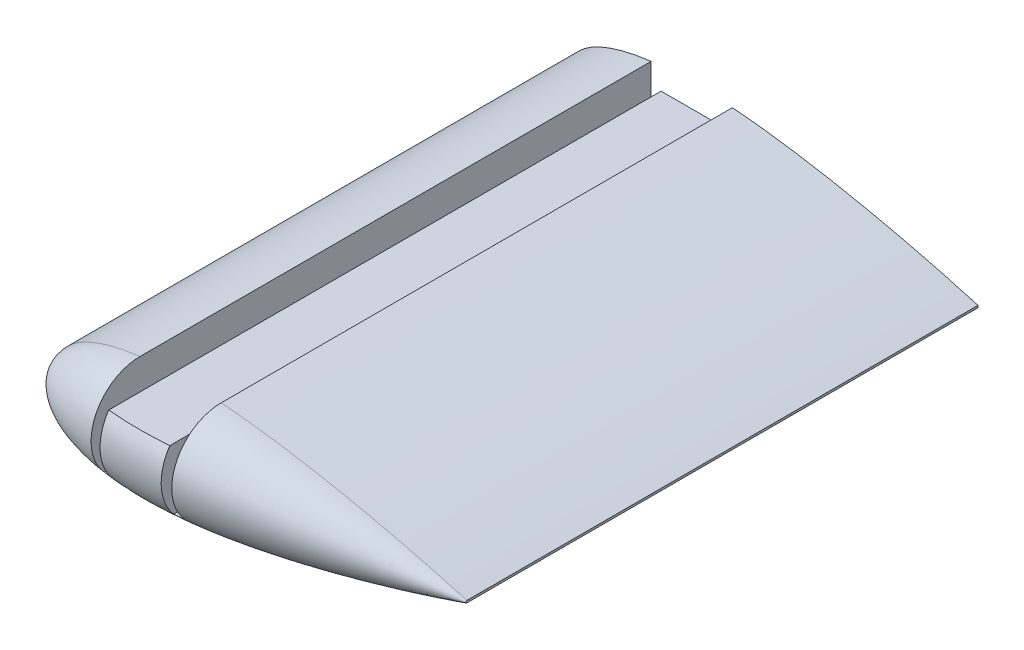
SolidWorks part; units mm, degrees
ref_plane "Спереди" through (0, 0, 0) normal (0, 0, 1) x (1, 0, 0)
ref_plane "Сверху" through (0, 0, 0) normal (0, 1, 0) x (1, 0, 0)
ref_plane "Справа" through (0, 0, 0) normal (1, 0, 0) x (0, 0, -1)
other "Configuration Table"
curve "Curve1"
  spline degree 3 poles (1, 0.0026, 0) (0.9995, 0.0028, 0) (0.9974, 0.0034, 0) (0.9928, 0.0047, 0) (0.9852, 0.0069, 0) (0.9746, 0.01, 0) (0.961, 0.0138, 0) (0.9446, 0.0183, 0) (0.9255, 0.0235, 0) (0.9037, 0.0292, 0) (0.8794, 0.0355, 0) (0.8529, 0.0421, 0) (0.8241, 0.0491, 0) (0.7933, 0.0562, 0) (0.7607, 0.0635, 0) (0.7266, 0.0709, 0) (0.691, 0.0782, 0) (0.6542, 0.0854, 0) (0.6165, 0.0923, 0) (0.5781, 0.0988, 0) (0.5392, 0.1049, 0) (0.5, 0.1104, 0) (0.4609, 0.1152, 0) (0.422, 0.1192, 0) (0.3836, 0.1222, 0) (0.3458, 0.1243, 0) (0.3091, 0.1252, 0) (0.2735, 0.1249, 0) (0.2392, 0.1234, 0) (0.2066, 0.1205, 0) (0.1758, 0.1164, 0) (0.147, 0.111, 0) (0.1203, 0.1043, 0) (0.096, 0.0965, 0) (0.0741, 0.0875, 0) (0.0549, 0.0774, 0) (0.0383, 0.0665, 0) (0.0245, 0.0546, 0) (0.0137, 0.042, 0) (0.0058, 0.0286, 0) (0.001, 0.0145, 0) (-0.0005, 0, 0) (0.001, -0.0145, 0) (0.0058, -0.0286, 0) (0.0137, -0.042, 0) (0.0245, -0.0546, 0) (0.0383, -0.0665, 0) (0.0549, -0.0774, 0) (0.0741, -0.0875, 0) (0.096, -0.0965, 0) (0.1203, -0.1043, 0) (0.147, -0.111, 0) (0.1758, -0.1164, 0) (0.2066, -0.1205, 0) (0.2392, -0.1234, 0) (0.2735, -0.1249, 0) (0.3091, -0.1252, 0) (0.3458, -0.1243, 0) (0.3836, -0.1222, 0) (0.422, -0.1192, 0) (0.4609, -0.1152, 0) (0.5, -0.1104, 0) (0.5392, -0.1049, 0) (0.5781, -0.0988, 0) (0.6165, -0.0923, 0) (0.6542, -0.0854, 0) (0.691, -0.0782, 0) (0.7266, -0.0709, 0) (0.7607, -0.0635, 0) (0.7933, -0.0562, 0) (0.8241, -0.0491, 0) (0.8529, -0.0421, 0) (0.8794, -0.0355, 0) (0.9037, -0.0292, 0) (0.9255, -0.0235, 0) (0.9446, -0.0183, 0) (0.961, -0.0138, 0) (0.9746, -0.01, 0) (0.9852, -0.0069, 0) (0.9928, -0.0047, 0) (0.9974, -0.0034, 0) (0.9995, -0.0028, 0) (1, -0.0026, 0) knots 0 0 0 0 0.000754 0.003013 0.006759 0.011967 0.018601 0.026614 0.035953 0.046555 0.058348 0.071256 0.085193 0.100071 0.115793 0.132259 0.149363 0.166997 0.185048 0.203403 0.221946 0.240561 0.259134 0.27755 0.295701 0.313483 0.330797 0.347552 0.363666 0.379065 0.393686 0.407475 0.420392 0.432406 0.443503 0.453686 0.462984 0.471456 0.479204 0.486388 0.493229 0.5 0.506771 0.513612 0.520796 0.528544 0.537016 0.546314 0.556497 0.567594 0.579608 0.592525 0.606314 0.620935 0.636334 0.652448 0.669203 0.686517 0.704299 0.72245 0.740866 0.759439 0.778054 0.796597 0.814952 0.833003 0.850637 0.867741 0.884207 0.899929 0.914807 0.928744 0.941652 0.953445 0.964047 0.973386 0.981399 0.988033 0.993241 0.996987 0.999246 1 1 1 1
sketch "Sketch2" plane through (0, 0, 0) normal (0, 0, 1) x (1, 0, 0)
  line L0 (55.999, 0.2099) -> (55.999, -0.2099) construction
  line L1 (55.999, 0) -> (-23.9777, 0) construction
  line L2 (-23.9777, 0) -> (-23.9777, 20.1567) construction
  line L3 (-7.5754, 10) -> (21.8908, 10) construction
  line L4 (55.999, 0.2099) -> (55.999, -0.2099)
  line L5 (0, 10) -> (0, -10) construction
  line L6 (55.999, -0.2099) -> (55.999, 14.9208) construction
  spline S1 degree 3 poles (55.999, 0.2099) (53.4639, 0.9505) (48.8039, 2.2339) (42.4289, 3.8199) (36.7434, 5.1209) (31.1997, 6.2872) (25.2824, 7.4075) (20.1765, 8.2452) (14.9796, 8.9749) (10.8215, 9.4486) (6.6974, 9.777) (3.6807, 9.9396) (0.7396, 10.0127) (-2.1078, 9.99) (-4.8439, 9.867) (-7.4522, 9.6409) (-9.9165, 9.3106) (-12.2218, 8.8772) (-14.354, 8.3437) (-16.3004, 7.7143) (-18.0494, 6.9954) (-19.5906, 6.1934) (-20.9154, 5.3156) (-22.0159, 4.3681) (-22.8849, 3.3565) (-23.5145, 2.285) (-23.8954, 1.1588) (-24.0187, 0) (-23.8954, -1.1588) (-23.5145, -2.285) (-22.8849, -3.3565) (-22.0159, -4.3681) (-20.9154, -5.3156) (-19.5906, -6.1934) (-18.0494, -6.9954) (-16.3004, -7.7143) (-14.354, -8.3437) (-12.2218, -8.8772) (-9.9165, -9.3106) (-7.4522, -9.6409) (-4.8439, -9.867) (-2.1078, -9.99) (0.7396, -10.0127) (3.6807, -9.9396) (7.7407, -9.7208) (12.9128, -9.2413) (19.1367, -8.4158) (25.2824, -7.4074) (31.1998, -6.2873) (37.5172, -4.9581) (44.7426, -3.2759) (51.0576, -1.6263) (54.945, -0.5178) (55.9579, -0.2219) (55.999, -0.2099) knots 0 0 0 0 0.046555 0.085193 0.115793 0.149363 0.185048 0.221946 0.240561 0.27755 0.295701 0.313483 0.330797 0.347552 0.363666 0.379065 0.393686 0.407475 0.420392 0.432406 0.443503 0.453686 0.462984 0.471456 0.479204 0.486388 0.493229 0.5 0.506771 0.513612 0.520796 0.528544 0.537016 0.546314 0.556497 0.567594 0.579608 0.592525 0.606314 0.620935 0.636334 0.652448 0.669203 0.686517 0.704299 0.740866 0.778054 0.814952 0.850637 0.884207 0.928744 0.981399 0.999246 1 1 1 1
  point P11 (0, 0)
  dimension "D1" = 20
extrude "Boss-Extrude1" add sketch "Sketch2" along normal blind 100
sketch "Sketch4" plane through (0, 0, 100) normal (0, 0, 1) x (1, 0, 0)
  line L0 (55.999, 0) -> (-23.9777, 0)
  line L1 (55.999, -0.2099) -> (55.999, 0.2099) construction
  line L3 (55.999, -0.2099) -> (55.999, 0.2099)
  line L4 (55.999, 0) -> (55.999, 0.2099)
  spline S0 degree 3 poles (55.999, 0.2099) (53.4639, 0.9505) (48.8039, 2.2339) (42.4289, 3.8199) (36.7434, 5.1209) (31.1997, 6.2872) (25.2824, 7.4075) (20.1765, 8.2452) (14.9796, 8.9749) (10.8215, 9.4486) (6.6974, 9.777) (3.6807, 9.9396) (0.7396, 10.0127) (-2.1078, 9.99) (-4.8439, 9.867) (-7.4522, 9.6409) (-9.9165, 9.3106) (-12.2218, 8.8772) (-14.354, 8.3437) (-16.3004, 7.7143) (-18.0494, 6.9954) (-19.5906, 6.1934) (-20.9154, 5.3156) (-22.0159, 4.3681) (-22.8849, 3.3565) (-23.5145, 2.285) (-23.8954, 1.1588) (-24.0187, 0) (-23.8954, -1.1588) (-23.5145, -2.285) (-22.8849, -3.3565) (-22.0159, -4.3681) (-20.9154, -5.3156) (-19.5906, -6.1934) (-18.0494, -6.9954) (-16.3004, -7.7143) (-14.354, -8.3437) (-12.2218, -8.8772) (-9.9165, -9.3106) (-7.4522, -9.6409) (-4.8439, -9.867) (-2.1078, -9.99) (0.7396, -10.0127) (3.6807, -9.9396) (7.7407, -9.7208) (12.9128, -9.2413) (19.1367, -8.4158) (25.2824, -7.4074) (31.1998, -6.2873) (37.5172, -4.9581) (44.7426, -3.2759) (51.0576, -1.6263) (54.945, -0.5178) (55.9579, -0.2219) (55.999, -0.2099) knots 0 0 0 0 0.046555 0.085193 0.115793 0.149363 0.185048 0.221946 0.240561 0.27755 0.295701 0.313483 0.330797 0.347552 0.363666 0.379065 0.393686 0.407475 0.420392 0.432406 0.443503 0.453686 0.462984 0.471456 0.479204 0.486388 0.493229 0.5 0.506771 0.513612 0.520796 0.528544 0.537016 0.546314 0.556497 0.567594 0.579608 0.592525 0.606314 0.620935 0.636334 0.652448 0.669203 0.686517 0.704299 0.740866 0.778054 0.814952 0.850637 0.884207 0.928744 0.981399 0.999246 1 1 1 1 construction
  spline S2 degree 3 poles (-635.3554, -2880.1705) (392.2047, -313.7808) (246.3383, -46.9116) (42.4289, 3.8199) (36.7434, 5.1209) (31.1997, 6.2872) (25.2824, 7.4075) (20.1765, 8.2452) (14.9796, 8.9749) (10.8215, 9.4486) (6.6974, 9.777) (3.6807, 9.9396) (0.7396, 10.0127) (-2.1078, 9.99) (-4.8439, 9.867) (-7.4522, 9.6409) (-9.9165, 9.3106) (-12.2218, 8.8772) (-14.354, 8.3437) (-16.3004, 7.7143) (-18.0494, 6.9954) (-19.5906, 6.1934) (-20.9154, 5.3156) (-22.0159, 4.3681) (-22.8849, 3.3565) (-23.5145, 2.285) (-23.8954, 1.1588) (-24.0187, 0) (-23.8954, -1.1588) (-23.5145, -2.285) (-22.8849, -3.3565) (-22.0159, -4.3681) (-20.9154, -5.3156) (-19.5906, -6.1934) (-18.0494, -6.9954) (-16.3004, -7.7143) (-14.354, -8.3437) (-12.2218, -8.8772) (-9.9165, -9.3106) (-7.4522, -9.6409) (-4.8439, -9.867) (-2.1078, -9.99) (0.7396, -10.0127) (3.6807, -9.9396) (7.7407, -9.7208) (12.9128, -9.2413) (19.1367, -8.4158) (25.2824, -7.4074) (31.1998, -6.2873) (37.5172, -4.9581) (44.7426, -3.2759) (51.0576, -1.6263) (81.4934, 7.0521) (107.6521, 19.7196) (975.9197, -2854.3918) knots -3.587955 -3.587955 -3.587955 -3.587955 0.046555 0.085193 0.115793 0.149363 0.185048 0.221946 0.240561 0.27755 0.295701 0.313483 0.330797 0.347552 0.363666 0.379065 0.393686 0.407475 0.420392 0.432406 0.443503 0.453686 0.462984 0.471456 0.479204 0.486388 0.493229 0.5 0.506771 0.513612 0.520796 0.528544 0.537016 0.546314 0.556497 0.567594 0.579608 0.592525 0.606314 0.620935 0.636334 0.652448 0.669203 0.686517 0.704299 0.740866 0.778054 0.814952 0.850637 0.884207 0.928744 0.981399 0.999246 1.486622 1.486622 1.486622 1.486622 only from (55.999, 0.2099) to (55.999, -0.2099)
  spline S3 degree 3 poles (55.999, 0.2099) (53.4639, 0.9505) (48.8039, 2.2339) (42.4289, 3.8199) (36.7434, 5.1209) (31.1997, 6.2872) (25.2824, 7.4075) (20.1765, 8.2452) (14.9796, 8.9749) (10.8215, 9.4486) (6.6974, 9.777) (3.6807, 9.9396) (0.7396, 10.0127) (-2.1078, 9.99) (-4.8439, 9.867) (-7.4522, 9.6409) (-9.9165, 9.3106) (-12.2218, 8.8772) (-14.354, 8.3437) (-16.3004, 7.7143) (-18.0494, 6.9954) (-19.5906, 6.1934) (-20.9154, 5.3156) (-22.0159, 4.3681) (-22.8849, 3.3565) (-23.5145, 2.285) (-23.8954, 1.1588) (-23.9777, 0.3849) (-23.9777, 0) knots 0 0 0 0 0.046555 0.085193 0.115793 0.149363 0.185048 0.221946 0.240561 0.27755 0.295701 0.313483 0.330797 0.347552 0.363666 0.379065 0.393686 0.407475 0.420392 0.432406 0.443503 0.453686 0.462984 0.471456 0.479204 0.486388 0.493229 0.5 0.5 0.5 0.5
  dimension "D1" = 0
revolve "Revolve1" add sketch "Sketch4" angle 180 about L0
sketch "Sketch3" plane through (0, 0, 0) normal (0, 0, -1) x (-1, 0, 0)
  line L0 (6, -6.5) -> (7.95, -6.5)
  line L2 (-6, -6.5) -> (-6, 5.5)
  line L3 (-6, 5.5) -> (6, 5.5)
  line L4 (6, -6.5) -> (6, 5.5)
  line L5 (-6, -6.5) -> (6, 5.5) construction
  line L6 (-6, 5.5) -> (6, -6.5) construction
  line L7 (7.95, -6.5) -> (7.95, 9.5637)
  line L8 (-6, -6.5) -> (-7.95, -6.5)
  line L9 (-7.95, -6.5) -> (-7.95, 9.6738)
  line L10 (-11.2468, 10) -> (11.5184, 10) construction
  line L11 (0, 0) -> (0, 6.0357) construction
  line L12 (-7.95, -6.5) -> (7.95, -6.5) construction
  spline S0 degree 3 poles (275.2851, -1947.3186) (-351.5026, -245.2226) (-218.8463, -40.0718) (-42.4289, 3.8199) (-36.7434, 5.1209) (-31.1997, 6.2872) (-25.2824, 7.4075) (-20.1765, 8.2452) (-14.9796, 8.9749) (-10.8215, 9.4486) (-6.6974, 9.777) (-3.6807, 9.9396) (-0.7396, 10.0127) (2.1078, 9.99) (4.8439, 9.867) (7.4522, 9.6409) (9.9165, 9.3106) (12.2218, 8.8772) (14.354, 8.3437) (16.3004, 7.7143) (18.0494, 6.9954) (19.5906, 6.1934) (20.9154, 5.3156) (22.0159, 4.3681) (22.8849, 3.3565) (23.5145, 2.285) (23.8954, 1.1588) (24.0187, 0) (23.8954, -1.1588) (23.5145, -2.285) (22.8849, -3.3565) (22.0159, -4.3681) (20.9154, -5.3156) (19.5906, -6.1934) (18.0494, -6.9954) (16.3004, -7.7143) (14.354, -8.3437) (12.2218, -8.8772) (9.9165, -9.3106) (7.4522, -9.6409) (4.8439, -9.867) (2.1078, -9.99) (-0.7396, -10.0127) (-3.6807, -9.9396) (-7.7407, -9.7208) (-12.9128, -9.2413) (-19.1367, -8.4158) (-25.2824, -7.4074) (-31.1998, -6.2873) (-37.5172, -4.9581) (-44.7426, -3.2759) (-51.0576, -1.6263) (-78.1348, 6.0944) (-101.2564, 16.704) (-685.5525, -1897.6172) knots -3.088599 -3.088599 -3.088599 -3.088599 0.046555 0.085193 0.115793 0.149363 0.185048 0.221946 0.240561 0.27755 0.295701 0.313483 0.330797 0.347552 0.363666 0.379065 0.393686 0.407475 0.420392 0.432406 0.443503 0.453686 0.462984 0.471456 0.479204 0.486388 0.493229 0.5 0.506771 0.513612 0.520796 0.528544 0.537016 0.546314 0.556497 0.567594 0.579608 0.592525 0.606314 0.620935 0.636334 0.652448 0.669203 0.686517 0.704299 0.740866 0.778054 0.814952 0.850637 0.884207 0.928744 0.981399 0.999246 1.425061 1.425061 1.425061 1.425061 only from (-55.999, 0.2099) to (-55.999, -0.2099) construction
  spline S1 degree 3 poles (-7.95, 9.6738) (-7.5253, 9.7065) (-6.0943, 9.8095) (-3.6807, 9.9396) (-0.7396, 10.0127) (2.1078, 9.99) (4.8439, 9.867) (6.7781, 9.6993) (7.7981, 9.5819) (7.95, 9.5637) knots 0.288193 0.288193 0.288193 0.288193 0.295701 0.313483 0.330797 0.347552 0.363666 0.379065 0.381762 0.381762 0.381762 0.381762
  point P0 (0, -0.5)
  point P13 (-6.975, -6.5)
  dimension "D1" = 12
  dimension "D2" = 12
  dimension "D3" = 1.95
  dimension "D4" = 1.95
  dimension "D5" = 16.5
extrude "Cut-Extrude1" cut sketch "Sketch3" against normal up to next
